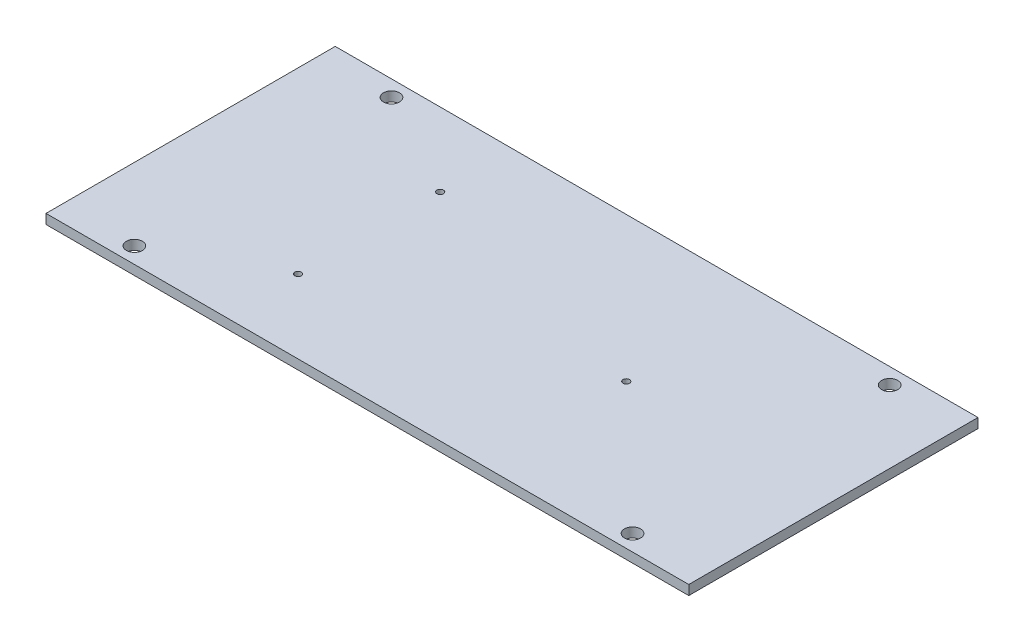
SolidWorks part; units mm, degrees
ref_plane "Front Plane" through (0, 0, 0) normal (0, 0, 1) x (1, 0, 0)
ref_plane "Top Plane" through (0, 0, 0) normal (0, 1, 0) x (1, 0, 0)
ref_plane "Right Plane" through (0, 0, 0) normal (1, 0, 0) x (0, 0, -1)
sketch "Sketch1" plane through (0, 0, 0) normal (0, 1, 0) x (1, 0, 0)
  line L1 (-100, -45) -> (100, -45)
  line L2 (-100, -45) -> (-100, 45)
  line L3 (-100, 45) -> (100, 45)
  line L4 (100, -45) -> (100, 45)
  line L5 (-100, -45) -> (100, 45) construction
  line L6 (-100, 45) -> (100, -45) construction
  point P0 (0, 0)
  dimension "D1" = 200
  dimension "D2" = 90
extrude "Boss-Extrude1" add sketch "Sketch1" along normal blind 3
sketch "Sketch2" plane through (0, 3, 0) normal (0, 1, 0) x (1, 0, 0)
  line L1 (-77.5, -40) -> (77.5, -40) construction
  line L2 (-77.5, -40) -> (-77.5, 40) construction
  line L3 (-77.5, 40) -> (77.5, 40) construction
  line L4 (77.5, -40) -> (77.5, 40) construction
  line L5 (-77.5, -40) -> (77.5, 40) construction
  line L6 (-77.5, 40) -> (77.5, -40) construction
  circle A0 centre (-77.5, 40) radius 2.5
  circle A1 centre (77.5, 40) radius 2.5
  circle A2 centre (77.5, -40) radius 2.5
  circle A3 centre (-77.5, -40) radius 2.5
  point P0 (0, 0)
  dimension "D1" = 5
  dimension "D2" = 80
  dimension "D3" = 155
extrude "Cut-Extrude1" cut sketch "Sketch2" against normal through all
sketch "Sketch3" plane through (0, 3, 0) normal (0, 1, 0) x (1, 0, 0)
  circle A0 centre (-44.45, 22.098) radius 1.016
  circle A1 centre (-44.45, -22.098) radius 1.016
  circle A2 centre (35.56, 0) radius 1.016
  arc A4 (35.56, 1.016) -> (35.56, -1.016) centre (35.56, 0) ccw construction
extrude "Cut-Extrude2" cut sketch "Sketch3" against normal through all
